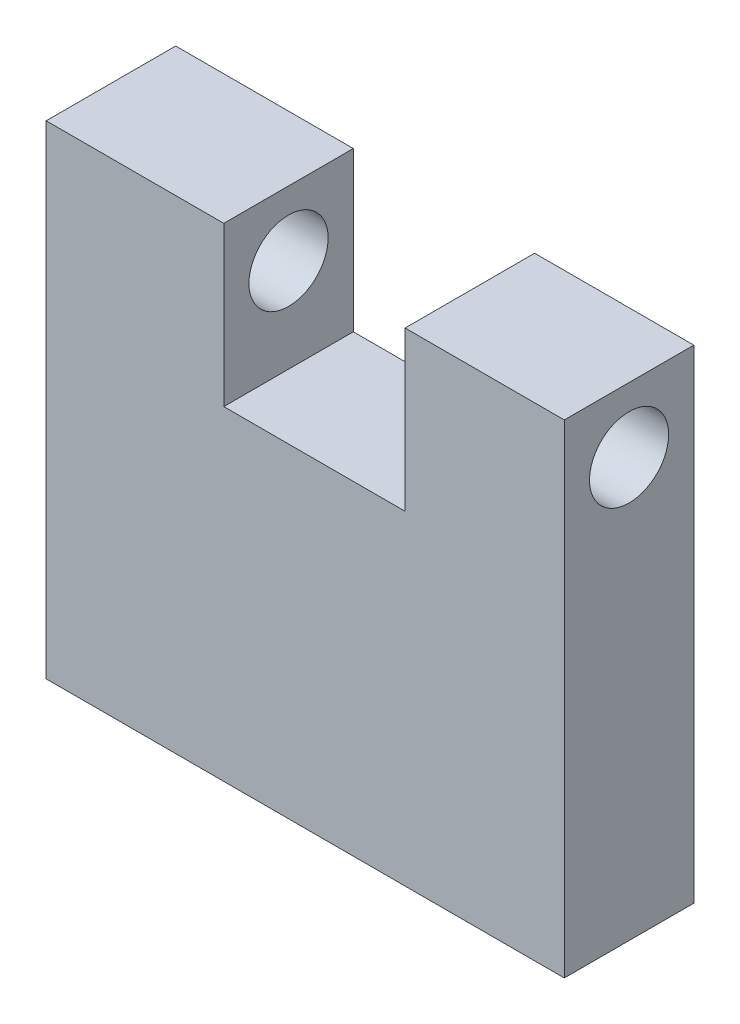
SolidWorks part; units mm, degrees
ref_plane "Front Plane" through (0, 0, 0) normal (0, 0, 1) x (1, 0, 0)
ref_plane "Top Plane" through (0, 0, 0) normal (0, 1, 0) x (1, 0, 0)
ref_plane "Right Plane" through (0, 0, 0) normal (1, 0, 0) x (0, 0, -1)
sketch "Sketch1" plane through (0, 0, 0) normal (0, 0, 1) x (1, 0, 0)
  line L1 (9.8308, -10.5695) -> (-8.4572, -10.5695)
  line L2 (9.8308, -10.5695) -> (9.8308, 6.4901)
  line L3 (9.8308, 6.4901) -> (4.2112, 6.4901)
  line L4 (-8.4572, -10.5695) -> (-8.4572, 6.4901)
  line L5 (9.8308, -10.5695) -> (-8.4572, 6.4901) construction
  line L6 (9.8308, 6.4901) -> (-8.4572, -10.5695) construction
  line L7 (-2.1886, 6.4901) -> (-2.1886, 0.8879)
  line L8 (-2.1886, 0.8879) -> (4.2112, 0.8879)
  line L9 (4.2112, 0.8879) -> (4.2112, 6.4901)
  line L10 (-2.1886, 6.4901) -> (-8.4572, 6.4901)
  point P0 (0, 0)
extrude "Boss-Extrude1" add sketch "Sketch1" along normal mid plane 4.572
sketch "Sketch3" plane through (9.8308, 0, 0) normal (1, 0, 0) x (0, 0, -1)
  line L0 (1.397, 4.2041) -> (2.286, 4.2041) construction
  line L1 (2.286, -10.5695) -> (2.286, 6.4901) construction
  line L2 (0, 5.6011) -> (0, 6.4901) construction
  line L3 (-2.286, 6.4901) -> (2.286, 6.4901) construction
  circle A0 centre (0, 4.2041) radius 1.397
  dimension "D1" = 2.794
extrude "Cut-Extrude1" cut sketch "Sketch3" against normal through all
ref_plane "Plane1" through (31.6195, -4.7422, -23.9005) normal (0.7198, -0.6496, 0.2449) x (-0.6746, -0.7378, 0.0258)
